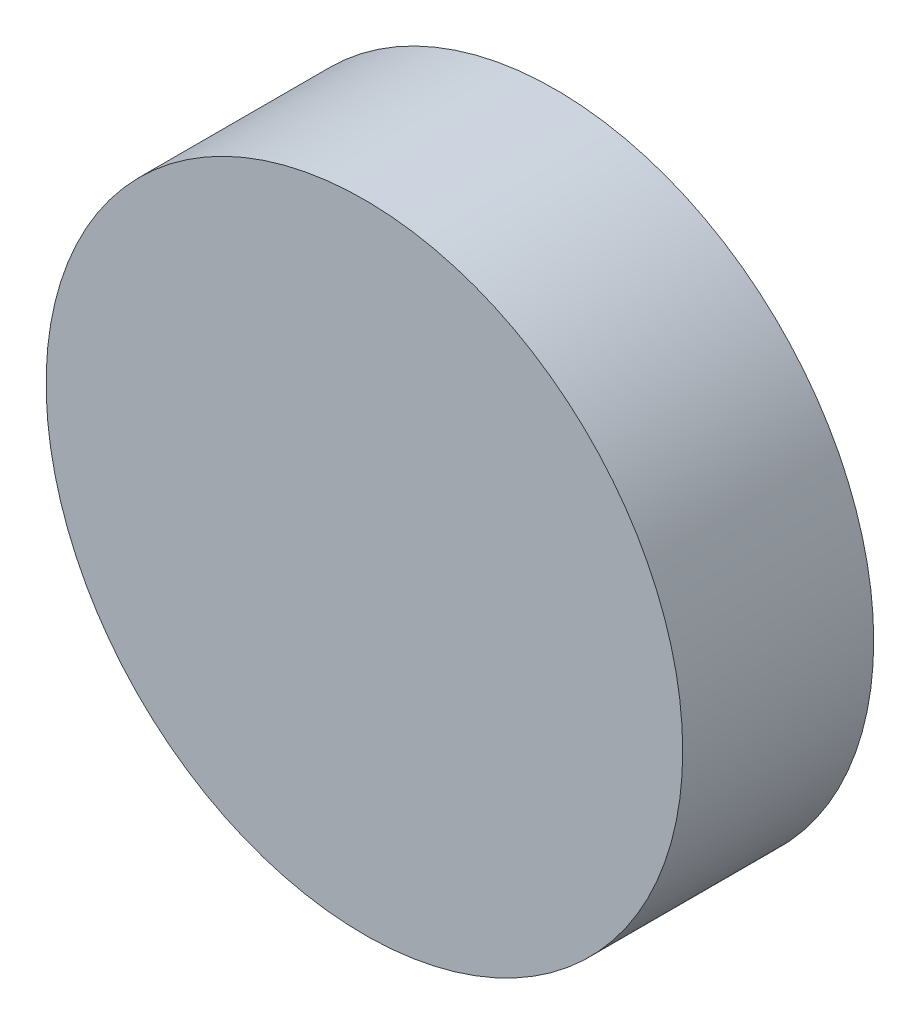
SolidWorks part; units mm, degrees
ref_plane "Front Plane" through (0, 0, 0) normal (0, 0, 1) x (1, 0, 0)
ref_plane "Top Plane" through (0, 0, 0) normal (0, 1, 0) x (1, 0, 0)
ref_plane "Right Plane" through (0, 0, 0) normal (1, 0, 0) x (0, 0, -1)
sketch "Sketch1" plane through (0, 0, 0) normal (0, 0, 1) x (1, 0, 0)
  circle A0 centre (0, 0) radius 100
  dimension "D1" = 200
extrude "Boss-Extrude1" add sketch "Sketch1" along normal blind 60
